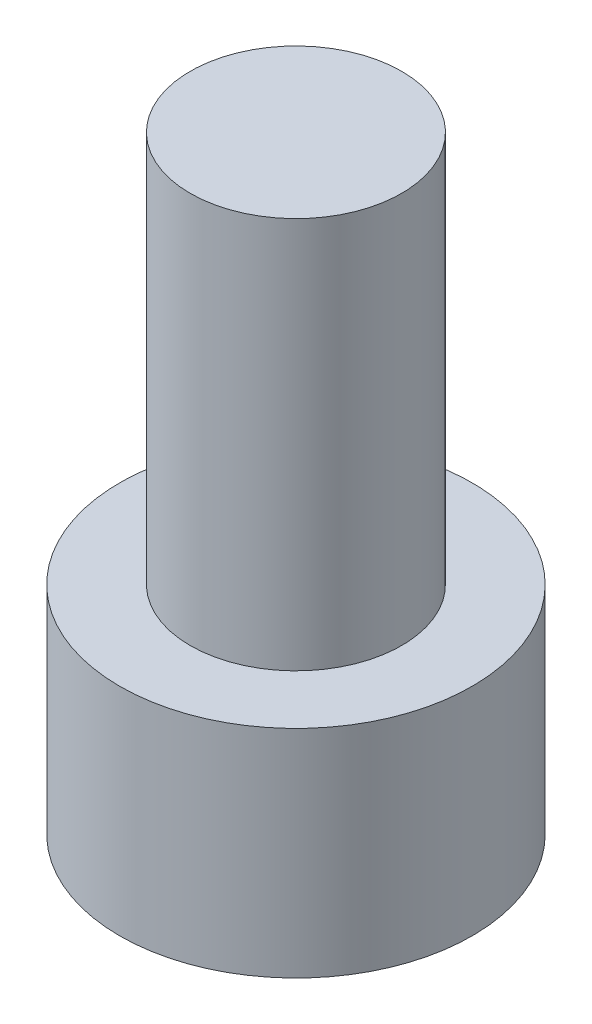
SolidWorks part; units mm, degrees
ref_plane "Front Plane" through (0, 0, 0) normal (0, 0, 1) x (1, 0, 0)
ref_plane "Top Plane" through (0, 0, 0) normal (0, 1, 0) x (1, 0, 0)
ref_plane "Right Plane" through (0, 0, 0) normal (1, 0, 0) x (0, 0, -1)
sketch "Sketch1" plane through (0, 0, 0) normal (0, 1, 0) x (1, 0, 0)
  circle A0 centre (0, 0) radius 2.8575
  dimension "D1" = 5.715
extrude "Boss-Extrude1" add sketch "Sketch1" along normal blind 3.5052
sketch "Sketch2" plane through (0, 0, 0) normal (0, -1, 0) x (1, 0, 0)
  line L1 (1.604, 0) -> (0.802, 1.3891)
  line L2 (0.802, 1.3891) -> (-0.802, 1.3891)
  line L3 (-0.802, 1.3891) -> (-1.604, 0)
  line L4 (-1.604, 0) -> (-0.802, -1.3891)
  line L5 (-0.802, -1.3891) -> (0.802, -1.3891)
  line L6 (0.802, -1.3891) -> (1.604, 0)
  circle A0 centre (0, 0) radius 1.3891 construction
  dimension "D1" = 2.7781
extrude "Cut-Extrude1" cut sketch "Sketch2" against normal blind 1.9558
sketch "Sketch3" plane through (0, 3.5052, 0) normal (0, 1, 0) x (1, 0, 0)
  circle A0 centre (0, 0) radius 1.7145
  dimension "D1" = 3.429
extrude "Boss-Extrude2" add sketch "Sketch3" along normal blind 6.35
